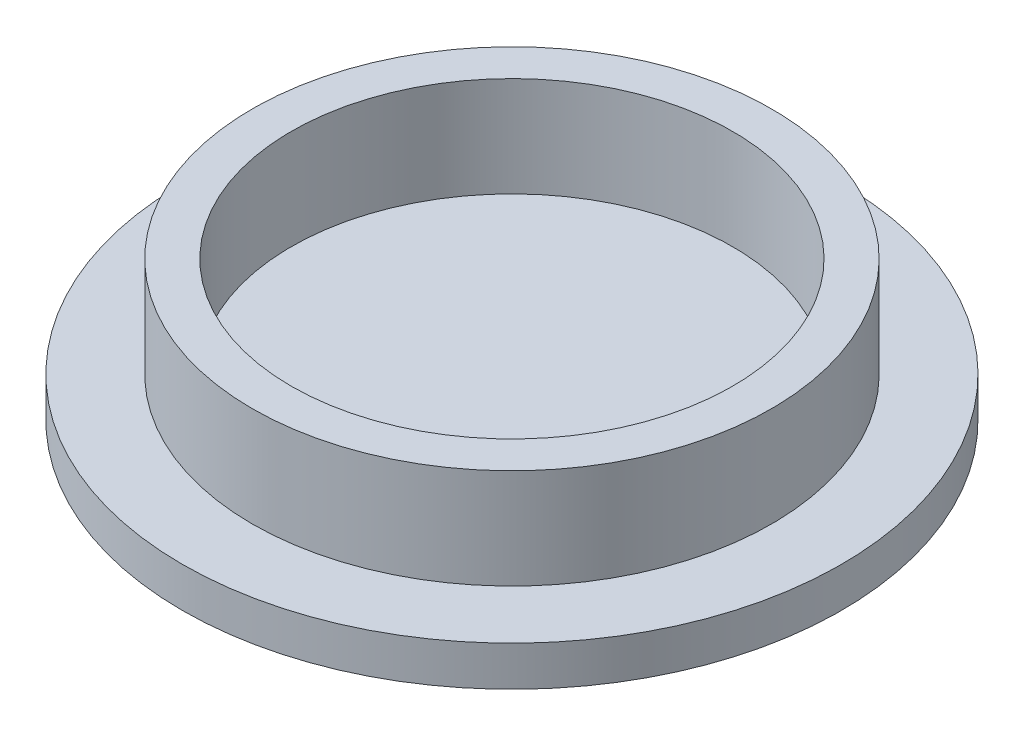
SolidWorks part; units mm, degrees
material "PLA"
ref_plane "Front Plane" through (0, 0, 0) normal (0, 0, 1) x (1, 0, 0)
ref_plane "Top Plane" through (0, 0, 0) normal (0, 1, 0) x (1, 0, 0)
ref_plane "Right Plane" through (0, 0, 0) normal (1, 0, 0) x (0, 0, -1)
sketch "Croquis1" plane through (0, 0, 0) normal (0, 1, 0) x (1, 0, 0)
  circle A0 centre (0, 0) radius 16.5
  dimension "D1" = 33
extrude "Saliente-Extruir1" add sketch "Croquis1" along normal blind 2
sketch "Croquis2" plane through (0, 2, 0) normal (0, 1, 0) x (1, 0, 0)
  circle A0 centre (0, 0) radius 11.05
  circle A1 centre (0, 0) radius 13
  dimension "D1" = 22.1
  dimension "D2" = 26
extrude "Saliente-Extruir2" add sketch "Croquis2" along normal blind 5
